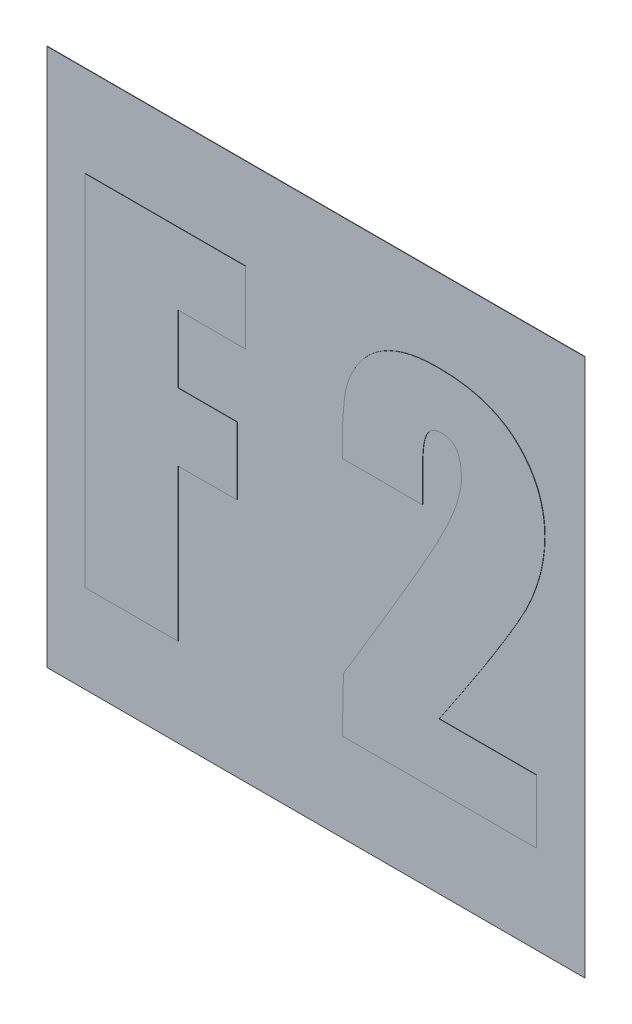
SolidWorks part; units mm, degrees
ref_plane "Plane1" through (0, 0, 0) normal (0, 0, 1) x (1, 0, 0)
ref_plane "Plane2" through (0, 0, 0) normal (0, 1, 0) x (1, 0, 0)
ref_plane "Plane3" through (0, 0, 0) normal (1, 0, 0) x (0, 0, -1)
sketch "Sketch1" plane through (0, 0, 0) normal (0, 0, 1) x (1, 0, 0)
  line L0 (-69.0098, 0) -> (69.0098, 0) construction
  line L1 (0, 52.3212) -> (0, -57.1323) construction
  line L2 (-7.5, 7.5) -> (7.5, 7.5)
  line L3 (-7.5, 7.5) -> (-7.5, -7.5)
  line L4 (7.5, 7.5) -> (7.5, -7.5)
  line L5 (-7.5, -7.5) -> (7.5, -7.5)
  point P8 (0, -7.5)
  point P11 (0, 7.5)
  point P12 (7.5, 0)
  point P13 (-7.5, 0)
  dimension "D1" = 15
  dimension "D2" = 15
extrude "Base-Extrude" add sketch "Sketch1" along normal blind 0.01
sketch "Sketch3" plane through (0, 0, 0.01) normal (0, 0, 1) x (1, 0, 0)
  text T0 "F 2" font "Impact" height in points 36
extrude "Boss-Extrude1" add sketch "Sketch3" along normal blind 0.01
